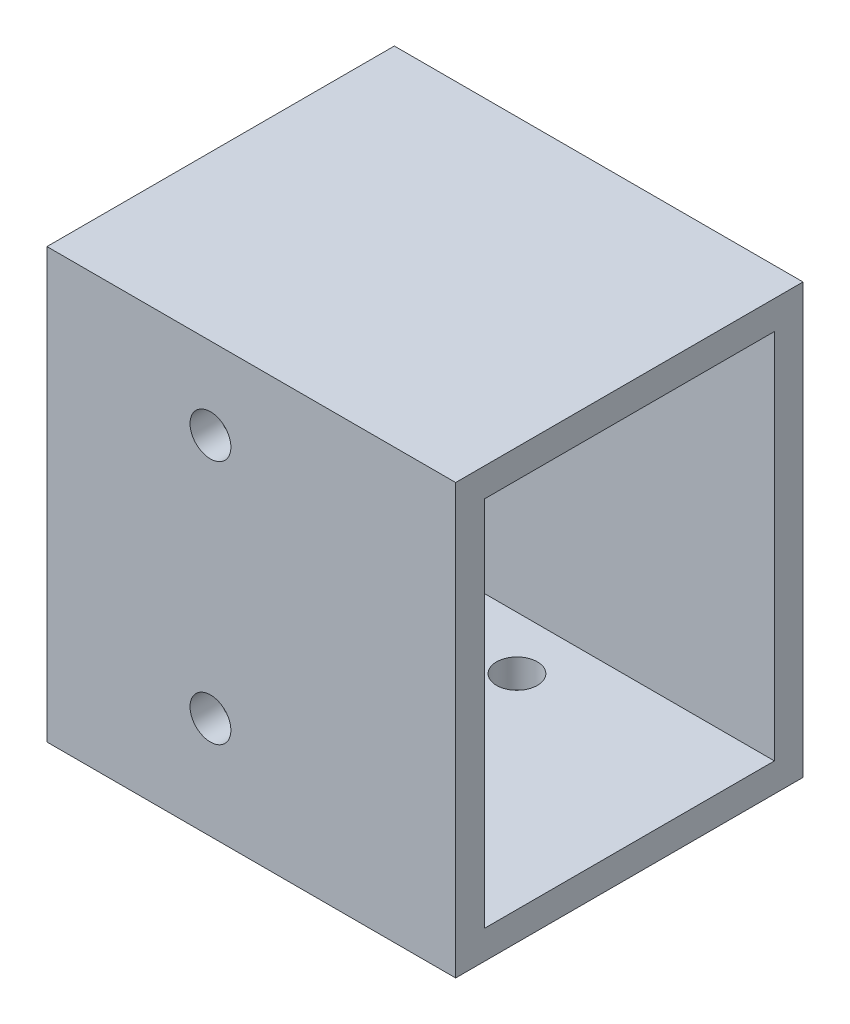
SolidWorks part; units mm, degrees
material "1060 Alloy"
ref_plane "Front Plane" through (0, 0, 0) normal (0, 0, 1) x (1, 0, 0)
ref_plane "Top Plane" through (0, 0, 0) normal (0, 1, 0) x (1, 0, 0)
ref_plane "Right Plane" through (0, 0, 0) normal (1, 0, 0) x (0, 0, -1)
sketch "Sketch1" plane through (0, 0, 0) normal (0, 1, 0) x (1, 0, 0)
  line L1 (-61.9583, -34.5966) -> (38.0417, -34.5966)
  line L2 (-61.9583, -34.5966) -> (-61.9583, 50.4034)
  line L3 (-61.9583, 50.4034) -> (38.0417, 50.4034)
  line L4 (38.0417, -34.5966) -> (38.0417, 50.4034)
  dimension "D1" = 100
  dimension "D2" = 85
extrude "Boss-Extrude1" add sketch "Sketch1" along normal blind 105
ref_plane "Plane1" through (38.0417, 0, 0) normal (1, 0, 0) x (0, 0, -1)
sketch "Sketch2" plane through (38.0417, 0, 0) normal (1, 0, 0) x (0, 0, -1)
  line L0 (50.4034, 105) -> (50.4034, 0) construction
  line L1 (-27.5966, 98) -> (43.4034, 98)
  line L2 (-27.5966, 98) -> (-27.5966, 7)
  line L3 (-27.5966, 7) -> (43.4034, 7)
  line L4 (43.4034, 98) -> (43.4034, 7)
  line L5 (-34.5966, 105) -> (-34.5966, 0) construction
  line L6 (-34.5966, 0) -> (50.4034, 0) construction
  line L7 (-34.5966, 105) -> (50.4034, 105) construction
  dimension "D1" = 7
  dimension "D2" = 7
  dimension "D3" = 7
  dimension "D4" = 7
extrude "Cut-Extrude1" cut sketch "Sketch2" against normal blind 90
ref_plane "Plane2" through (0, 0, 34.5966) normal (0, 0, 1) x (1, 0, 0)
sketch "Sketch3" plane through (0, 0, 34.5966) normal (0, 0, 1) x (1, 0, 0)
  line L0 (-61.9583, 105) -> (38.0417, 105) construction
  line L1 (-61.9583, 105) -> (-61.9583, 0) construction
  point P0 (-21.9583, 85)
  point P1 (-21.9583, 25)
  dimension "D1" = 20
  dimension "D2" = 40
  dimension "D3" = 60
  dimension "D4" = 40
hole_wizard "M10x1.0 Tapped Hole1" positions "3DSketch1" profile "Sketch4" tap size "M10x1.0" standard "ANSI Metric"
sketch3d "3DSketch1"
  point P0 (-21.9583, 85, 34.5966)
  point P3 (-21.9583, 25, 34.5966)
sketch "Sketch4" plane through (-21.9583, 85, 34.5966) normal (1, 0, 0) x (0, -1, 0)
  line L0 (0, 0) -> (0, 25.7039)
  line L1 (0, 25.7039) -> (4.5, 23)
  line L2 (4.5, 23) -> (4.5, 20)
  line L3 (4.5, 20) -> (5, 20)
  line L4 (5, 20) -> (5, 0)
  line L5 (5, 0) -> (0, 0)
  line L10 (0, 25.7039) -> (-4.5, 23) construction
  line L11 (0, -6.35) -> (0, 107.95) construction
  dimension "Tap Drill Dia." = 9
  dimension "Tap Drill Depth" = 23
  dimension "Thread Major Dia." = 10
  dimension "Thread Depth" = 20
  dimension "Drill Angle" = 118
sketch "Sketch5" plane through (0, 0, 0) normal (0, -1, 0) x (1, 0, 0)
  line L0 (38.0417, 34.5966) -> (38.0417, -50.4034) construction
  line L2 (38.0417, -50.4034) -> (-61.9583, -50.4034) construction
  point P0 (-11.9583, -30.4034)
  dimension "D1" = 50
  dimension "D2" = 20
hole_wizard "M10x1.0 Tapped Hole2" positions "3DSketch2" profile "Sketch6" tap size "M10x1.0" standard "ANSI Metric"
sketch3d "3DSketch2"
  point P0 (-11.9583, 0, -30.4034)
sketch "Sketch6" plane through (-11.9583, 0, -30.4034) normal (1, 0, 0) x (0, 0, -1)
  line L0 (0, 0) -> (0, 25.7039)
  line L1 (0, 25.7039) -> (4.5, 23)
  line L2 (4.5, 23) -> (4.5, 20)
  line L3 (4.5, 20) -> (5, 20)
  line L4 (5, 20) -> (5, 0)
  line L5 (5, 0) -> (0, 0)
  line L10 (0, 25.7039) -> (-4.5, 23) construction
  line L11 (0, -6.35) -> (0, 107.95) construction
  dimension "Tap Drill Dia." = 9
  dimension "Tap Drill Depth" = 23
  dimension "Thread Major Dia." = 10
  dimension "Thread Depth" = 20
  dimension "Drill Angle" = 118
ref_plane "Plane3" through (-61.9583, 0, 0) normal (-1, 0, 0) x (0, 0, 1)
sketch "Sketch7" plane through (-61.9583, 0, 0) normal (-1, 0, 0) x (0, 0, 1)
  point P6 (-7.9034, 52.5)
  point P7 (-7.9034, 67.5)
  point P8 (-7.9034, 37.5)
  dimension "D1" = 15
  dimension "D2" = 15
hole_wizard "M10x1.0 Tapped Hole3" positions "Sketch13" profile "Sketch12" tap size "M10x1.0" standard "ANSI Metric"
sketch "Sketch13" plane through (-61.9583, 0, 0) normal (-1, 0, 0) x (0, 0, 1)
  point P0 (-7.9034, 37.5)
  point P3 (-7.9034, 52.5)
  point P6 (-7.9034, 67.5)
sketch "Sketch12" plane through (-61.9583, 37.5, -7.9034) normal (0, 1, 0) x (0, 0, 1)
  line L0 (0, 0) -> (0, 25.7039)
  line L1 (0, 25.7039) -> (4.5, 23)
  line L2 (4.5, 23) -> (4.5, 20)
  line L3 (4.5, 20) -> (5, 20)
  line L4 (5, 20) -> (5, 0)
  line L5 (5, 0) -> (0, 0)
  line L10 (0, 25.7039) -> (-4.5, 23) construction
  line L11 (0, -6.35) -> (0, 107.95) construction
  dimension "Tap Drill Dia." = 9
  dimension "Tap Drill Depth" = 23
  dimension "Thread Major Dia." = 10
  dimension "Thread Depth" = 20
  dimension "Drill Angle" = 118
